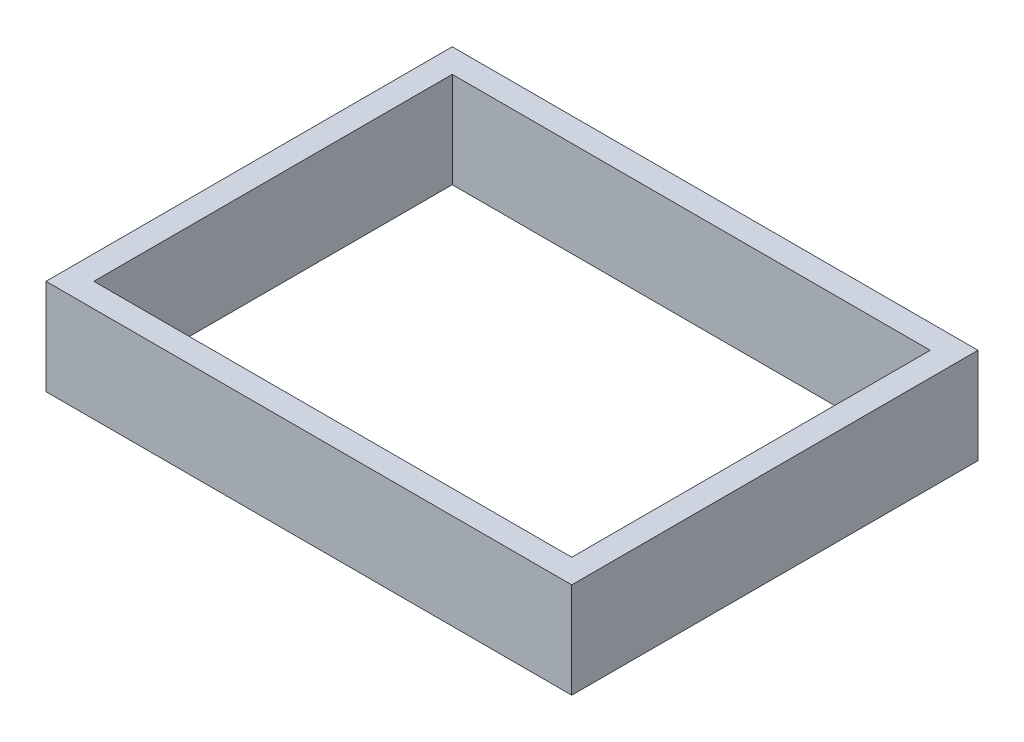
SolidWorks part; units mm, degrees
ref_plane "Front Plane" through (0, 0, 0) normal (0, 0, 1) x (1, 0, 0)
ref_plane "Top Plane" through (0, 0, 0) normal (0, 1, 0) x (1, 0, 0)
ref_plane "Right Plane" through (0, 0, 0) normal (1, 0, 0) x (0, 0, -1)
sketch "Sketch1" plane through (0, 0, 0) normal (0, 1, 0) x (1, 0, 0)
  line L1 (-60.4643, 91.9237) -> (139.5357, 91.9237)
  line L2 (-60.4643, 91.9237) -> (-60.4643, -58.0763)
  line L3 (-60.4643, -58.0763) -> (139.5357, -58.0763)
  line L4 (139.5357, 91.9237) -> (139.5357, -58.0763)
  line L5 (-70.4643, 101.9237) -> (149.5357, 101.9237)
  line L6 (-70.4643, 101.9237) -> (-70.4643, -68.0763)
  line L7 (-70.4643, -68.0763) -> (149.5357, -68.0763)
  line L8 (149.5357, 101.9237) -> (149.5357, -68.0763)
  dimension "D1" = 10
  dimension "D2" = 10
  dimension "D3" = 10
  dimension "D4" = 10
  dimension "D5" = 150
  dimension "D6" = 200
extrude "Boss-Extrude1" add sketch "Sketch1" along normal blind 40 contours L2 L1 L4 L3 | L6 L5 L8 L7
